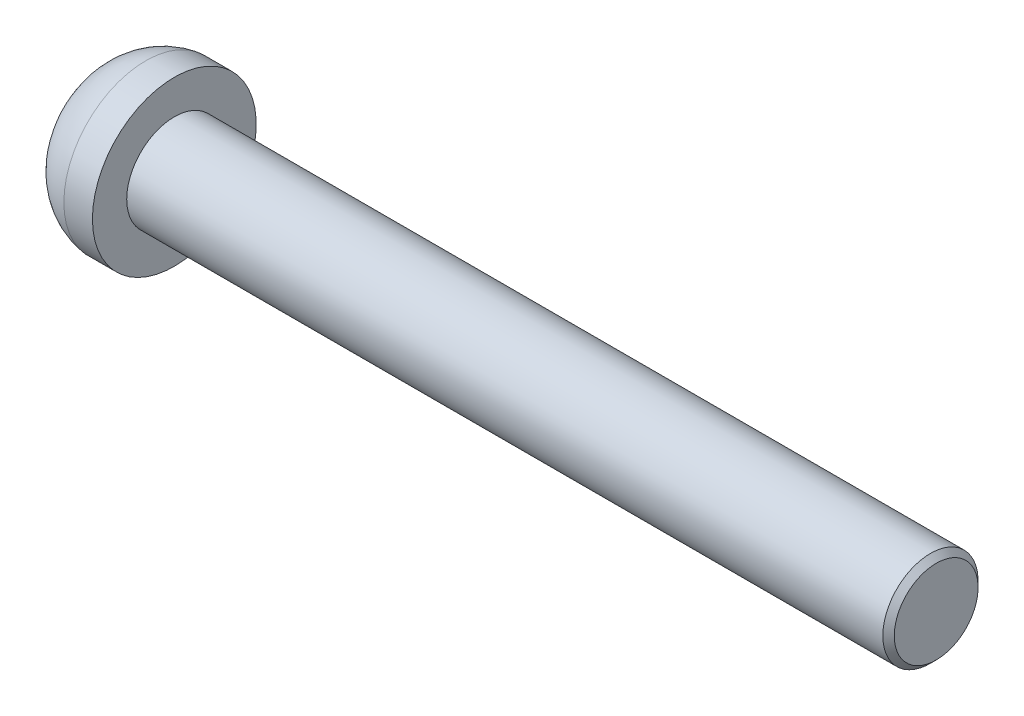
SolidWorks part; units mm, degrees
ref_plane "Front Plane" through (0, 0, 0) normal (0, 0, 1) x (1, 0, 0)
ref_plane "Top Plane" through (0, 0, 0) normal (0, 1, 0) x (1, 0, 0)
ref_plane "Right Plane" through (0, 0, 0) normal (1, 0, 0) x (0, 0, -1)
sketch "Sketch1" plane through (0, 0, 0) normal (0, 0, 1) x (1, 0, 0)
  line L0 (0, 0) -> (44, 0)
  line L1 (0, 0) -> (0, 2.5)
  line L2 (2.5, 4.3) -> (4, 4.3)
  line L3 (4, 4.3) -> (4, 2.5)
  line L4 (4, 2.5) -> (44, 2.5)
  line L5 (44, 2.5) -> (44, 0)
  arc A2 (0, 2.5) -> (2.5, 4.3) centre (2.9619, 1.0224) cw
  dimension "D6" = 2.5
  dimension "D1" = 40
  dimension "D2" = 2.5
  dimension "D3" = 4.3
  dimension "D4" = 1.5
  dimension "D5" = 4
revolve "Revolve1" add sketch "Sketch1" angle 360 about L0
chamfer "Chamfer1" distance 0.3 angle 45 1 edges at (44, 0, 2.5)
sketch "Sketch2" plane through (0, 0, 0) normal (-1, 0, 0) x (0, 0, 1)
  line L1 (0, 2.3094) -> (-2, 1.1547)
  line L2 (-2, 1.1547) -> (-2, -1.1547)
  line L3 (-2, -1.1547) -> (0, -2.3094)
  line L4 (0, -2.3094) -> (2, -1.1547)
  line L5 (2, -1.1547) -> (2, 1.1547)
  line L6 (2, 1.1547) -> (0, 2.3094)
  circle A0 centre (0, 0) radius 2 construction
  dimension "D1" = 4
extrude "Cut-Extrude1" cut sketch "Sketch2" against normal blind 2
